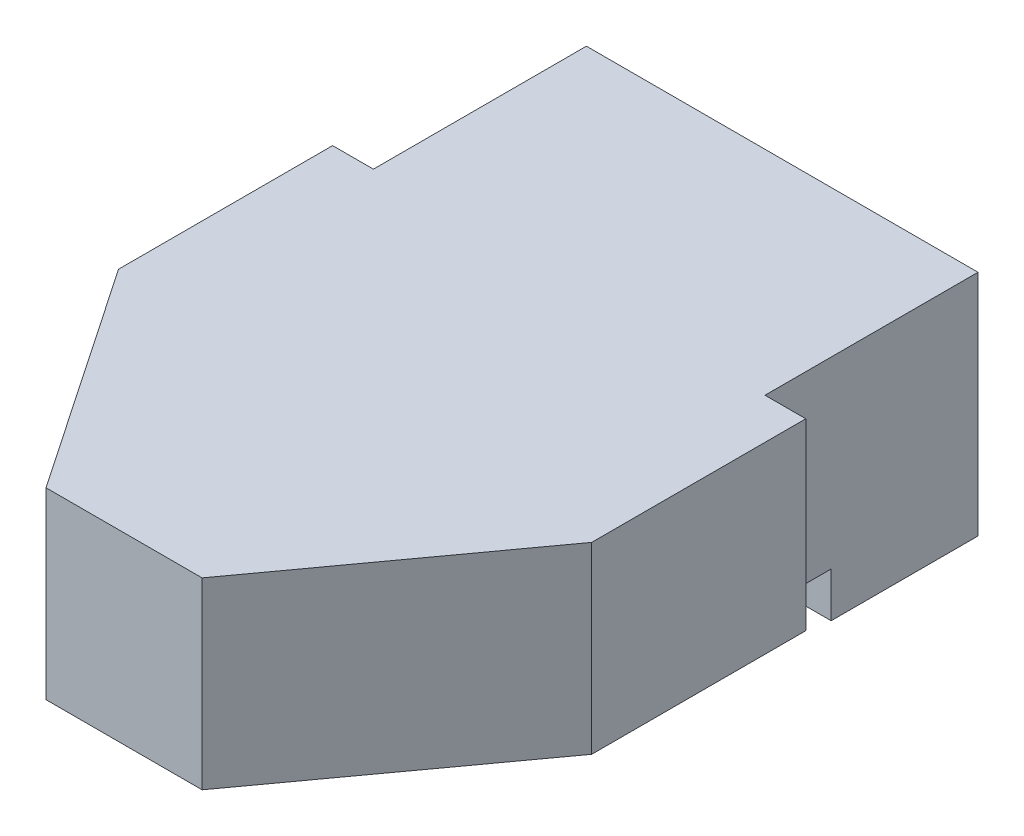
SolidWorks part; units mm, degrees
ref_plane "Front Plane" through (0, 0, 0) normal (0, 0, 1) x (1, 0, 0)
ref_plane "Top Plane" through (0, 0, 0) normal (0, 1, 0) x (1, 0, 0)
ref_plane "Right Plane" through (0, 0, 0) normal (1, 0, 0) x (0, 0, -1)
sketch "Sketch1" plane through (0, 0, 0) normal (0, 1, 0) x (1, 0, 0)
  line L0 (170.4445, 535.7431) -> (845.9285, 535.7431) construction
  line L3 (8.6929, 39.0507) -> (32.6929, 39.0507)
  line L4 (32.6929, 39.0507) -> (32.6929, 25.9954)
  line L5 (32.6929, 25.9954) -> (35.1929, 25.9954)
  line L6 (35.1929, 25.9954) -> (35.1929, 12.8755)
  line L7 (35.1929, 12.8755) -> (25.1383, -0.9493)
  line L8 (25.1383, -0.9493) -> (15.5712, -0.9493)
  line L9 (15.5712, -0.9493) -> (6.1929, 12.8755)
  line L10 (6.1929, 12.8755) -> (6.1929, 25.9954)
  line L11 (6.1929, 25.9954) -> (8.6929, 25.9954)
  line L12 (8.6929, 25.9954) -> (8.6929, 39.0507)
  line L13 (8.6929, 39.0507) -> (8.7972, 39.0815)
  dimension "D1" = 40
  dimension "D2" = 29
  dimension "D3" = 24
  dimension "D4" = 2.5
  dimension "D5" = 2.5
  dimension "D6" = 8.7972
  dimension "D7" = 15.5712
  dimension "D8" = 25.1383
extrude "Boss-Extrude1" add sketch "Sketch1" along normal blind 14 contours L3 L4 L5 L6 L7 L8 L9 L10 L11 L12
sketch "Sketch2" plane through (0, 0, 0) normal (0, -1, 0) x (1, 0, 0)
  line L3 (8.6929, -39.0507) -> (32.6929, -39.0507) construction
  line L4 (8.6929, -25.9954) -> (8.6929, -39.0507) construction
  circle A0 centre (20.5, -18) radius 2.25
  dimension "D1" = 4.5
  dimension "D2" = 11.8071
  dimension "D3" = 24
  dimension "D4" = 13.0553
  dimension "D5" = 21.0507
extrude "Boss-Extrude2" add sketch "Sketch2" along normal blind 2.75
sketch "Sketch4" plane through (0, 0, 0) normal (0, -1, 0) x (-1, 0, 0)
  line L0 (-8.6929, 30.0507) -> (-8.6929, 25.9954)
  line L1 (-8.6929, 25.9954) -> (-6.1929, 25.9954)
  line L2 (-8.6929, 30.0507) -> (-32.6929, 30.0507)
  line L3 (-8.6929, 25.9954) -> (-8.6929, 39.0507) construction
  line L4 (-32.6929, 39.0507) -> (-32.6929, 25.9954) construction
  line L5 (-6.1929, 25.9954) -> (-6.1929, 12.8755)
  line L6 (-6.1929, 12.8755) -> (-15.5712, -0.9493)
  line L7 (-15.5712, -0.9493) -> (-25.1383, -0.9493)
  line L8 (-25.1383, -0.9493) -> (-35.1929, 12.8755)
  line L9 (-35.1929, 12.8755) -> (-35.1929, 25.9954)
  line L10 (-35.1929, 25.9954) -> (-32.6929, 25.9954)
  line L11 (-32.6929, 25.9954) -> (-32.6929, 30.0507)
  line L12 (-35.1929, 25.9954) -> (-35.1929, 12.8755) construction
  line L13 (-32.6929, 25.9954) -> (-35.1929, 25.9954) construction
  circle A0 centre (-20.5, 18) radius 2.25
  dimension "D1" = 4.5
  dimension "D2" = 14.6929
  dimension "D3" = 4.0553
  dimension "D4" = 7.9954
extrude "Cut-Extrude1" cut sketch "Sketch4" against normal blind 2.75
